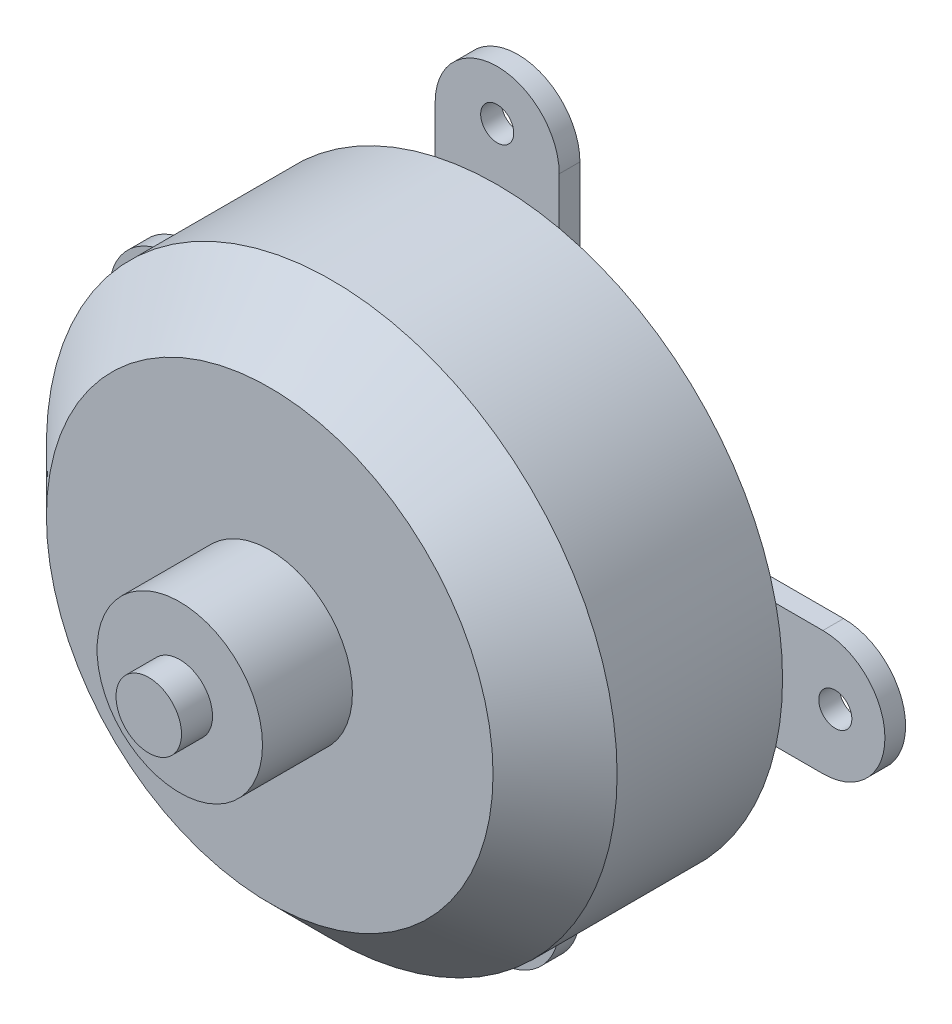
SolidWorks part; units mm, degrees
ref_plane "Plan de face" through (0, 0, 0) normal (0, 0, 1) x (1, 0, 0)
ref_plane "Plan de dessus" through (0, 0, 0) normal (0, 1, 0) x (1, 0, 0)
ref_plane "Plan de droite" through (0, 0, 0) normal (1, 0, 0) x (0, 0, -1)
sketch "Esquisse3" plane through (0, 0, 0) normal (0, 0, 1) x (1, 0, 0)
  line L0 (-44.6387, 23.9619) -> (-44.6387, 11.2119)
  line L1 (-44.6387, 11.2119) -> (-57.3887, 11.2119)
  line L2 (-57.3887, 5.2119) -> (-44.6387, 5.2119)
  line L3 (-44.6387, 5.2119) -> (-44.6387, -7.5381)
  line L4 (-38.6387, -7.5381) -> (-38.6387, 5.2119)
  line L5 (-38.6387, 5.2119) -> (-25.8887, 5.2119)
  line L6 (-38.6387, 11.2119) -> (-25.8887, 11.2119)
  line L7 (-38.6387, 11.2119) -> (-38.6387, 23.9619)
  line L8 (-57.3887, 11.2119) -> (-57.3887, 5.2119)
  line L9 (-44.6387, -7.5381) -> (-38.6387, -7.5381)
  line L10 (-25.8887, 5.2119) -> (-25.8887, 11.2119)
  line L11 (-44.6387, 23.9619) -> (-38.6387, 23.9619)
  dimension "D9" = 12.75
  dimension "D10" = 12.75
  dimension "D1" = 6
  dimension "D2" = 12.75
  dimension "D3" = 12.75
  dimension "D4" = 6
  dimension "D5" = 12.75
  dimension "D6" = 12.75
  dimension "D7" = 12.75
  dimension "D8" = 12.75
extrude "Boss.-Extru.2" add sketch "Esquisse3" along normal blind 1
sketch "Esquisse4" plane through (0, 0, 1) normal (0, 0, 1) x (1, 0, 0)
  line L0 (-38.6387, 23.9619) -> (-44.6387, 23.9619) construction
  line L1 (-25.8887, 5.2119) -> (-25.8887, 11.2119) construction
  line L2 (-44.6387, -7.5381) -> (-38.6387, -7.5381) construction
  line L3 (-57.3887, 11.2119) -> (-57.3887, 5.2119) construction
  circle A0 centre (-41.6387, 23.9619) radius 3
  circle A1 centre (-25.8887, 8.2119) radius 3
  circle A2 centre (-41.6387, -7.5381) radius 3
  circle A3 centre (-57.3887, 8.2119) radius 3
extrude "Boss.-Extru.5" add sketch "Esquisse4" against normal blind 1
sketch "Esquisse8" plane through (0, 0, 1) normal (0, 0, 1) x (1, 0, 0)
  circle A0 centre (-41.6387, 8.2119) radius 13.8
  arc A1 (-25.8887, 5.2119) -> (-25.8887, 11.2119) centre (-25.8887, 8.2119) ccw construction
  arc A3 (-44.6387, -7.5381) -> (-38.6387, -7.5381) centre (-41.6387, -7.5381) ccw construction
  point P2 (-22.8887, 8.2119)
  point P6 (-41.6387, -10.5381)
  dimension "D1" = 18.75
  dimension "D3" = 27.6
  dimension "D2" = 18.75
hole_wizard "Trou pour taraudage pour trou taraudé M2x0.41" positions "Esquisse12" profile "Esquisse11" hole size "M2x0.4" standard "Ansi Métrique"
sketch "Esquisse12" plane through (0, 0, 1) normal (0, 0, 1) x (1, 0, 0)
  line L0 (-44.6387, 23.9619) -> (-44.6387, 11.2119) construction
  line L1 (-25.8887, 11.2119) -> (-38.6387, 11.2119) construction
  line L2 (-38.6387, -7.5381) -> (-38.6387, 5.2119) construction
  line L3 (-44.6387, 11.2119) -> (-57.3887, 11.2119) construction
  arc A0 (-38.6387, 23.9619) -> (-44.6387, 23.9619) centre (-41.6387, 23.9619) ccw construction
  arc A1 (-25.8887, 5.2119) -> (-25.8887, 11.2119) centre (-25.8887, 8.2119) ccw construction
  arc A3 (-44.6387, -7.5381) -> (-38.6387, -7.5381) centre (-41.6387, -7.5381) ccw construction
  arc A4 (-57.3887, 11.2119) -> (-57.3887, 5.2119) centre (-57.3887, 8.2119) ccw construction
  point P1 (-41.6387, 24.5619)
  point P3 (-25.2887, 8.2119)
  point P5 (-41.6387, -8.1381)
  point P7 (-57.9887, 8.2119)
  point P19 (-41.6387, 26.9619)
  point P23 (-22.8887, 8.2119)
  point P31 (-41.6387, -10.5381)
  point P35 (-60.3887, 8.2119)
  dimension "D1" = 3
  dimension "D2" = 3
  dimension "D3" = 3
  dimension "D4" = 3
  dimension "D5" = 2.4
  dimension "D6" = 2.4
  dimension "D7" = 2.4
  dimension "D8" = 2.4
sketch "Esquisse11" plane through (-41.6387, 24.5619, 1) normal (1, 0, 0) x (0, -1, 0)
  line L0 (0, 0) -> (0, 10.4807)
  line L1 (0, 10.4807) -> (0.8, 10)
  line L2 (0.8, 10) -> (0.8, 0)
  line L5 (0.8, 0) -> (0, 0)
  line L10 (0, 10.4807) -> (-0.8, 10) construction
  line L11 (0, -6.35) -> (0, 107.95) construction
  dimension "Diamètre du perçage" = 1.6
  dimension "Profondeur du perçage" = 10
  dimension "Angle de pointe" = 118
extrude "Boss.-Extru.6" add sketch "Esquisse8" along normal blind 11
chamfer "Chanfrein1" distance 3 angle 45 1 edges at (-27.8387, 8.2119, 12)
sketch "Esquisse13" plane through (0, 0, 12) normal (0, 0, 1) x (1, 0, 0)
  circle A0 centre (-41.6387, 8.2119) radius 4
  arc A1 (-38.6387, 23.9619) -> (-44.6387, 23.9619) centre (-41.6387, 23.9619) ccw construction
  arc A3 (-25.8887, 5.2119) -> (-25.8887, 11.2119) centre (-25.8887, 8.2119) ccw construction
  point P2 (-41.6387, 26.9619)
  point P9 (-22.8887, 8.2119)
  dimension "D1" = 18.75
  dimension "D2" = 18.75
extrude "Boss.-Extru.7" add sketch "Esquisse13" along normal blind 4.35
sketch "Esquisse14" plane through (0, 0, 16.35) normal (0, 0, 1) x (1, 0, 0)
  circle A0 centre (-41.6387, 8.2119) radius 1.5835
  arc A1 (-25.8887, 5.2119) -> (-25.8887, 11.2119) centre (-25.8887, 8.2119) ccw construction
  arc A3 (-44.6387, -7.5381) -> (-38.6387, -7.5381) centre (-41.6387, -7.5381) ccw construction
  point P2 (-22.8887, 8.2119)
  point P8 (-41.6387, -10.5381)
  dimension "D1" = 18.75
  dimension "D2" = 18.75
extrude "Boss.-Extru.8" add sketch "Esquisse14" along normal blind 1.5
